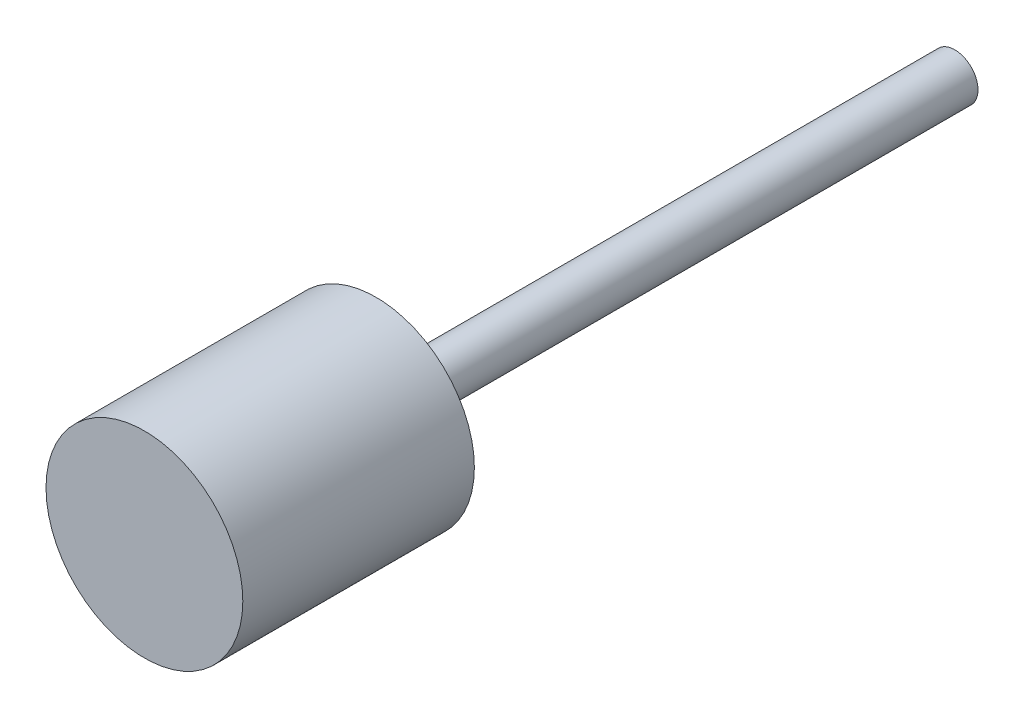
SolidWorks part; units mm, degrees
ref_plane "Front Plane" through (0, 0, 0) normal (0, 0, 1) x (1, 0, 0)
ref_plane "Top Plane" through (0, 0, 0) normal (0, 1, 0) x (1, 0, 0)
ref_plane "Right Plane" through (0, 0, 0) normal (1, 0, 0) x (0, 0, -1)
sketch "Sketch1" plane through (0, 0, 0) normal (0, 0, 1) x (1, 0, 0)
  circle A0 centre (0, 0) radius 2
  dimension "D1" = 4
extrude "Boss-Extrude1" add sketch "Sketch1" along normal blind 50
sketch "Sketch2" plane through (0, 0, 50) normal (0, 0, 1) x (1, 0, 0)
  circle A0 centre (0, 0) radius 8.5
  dimension "D1" = 17
extrude "Boss-Extrude2" add sketch "Sketch2" along normal blind 20
